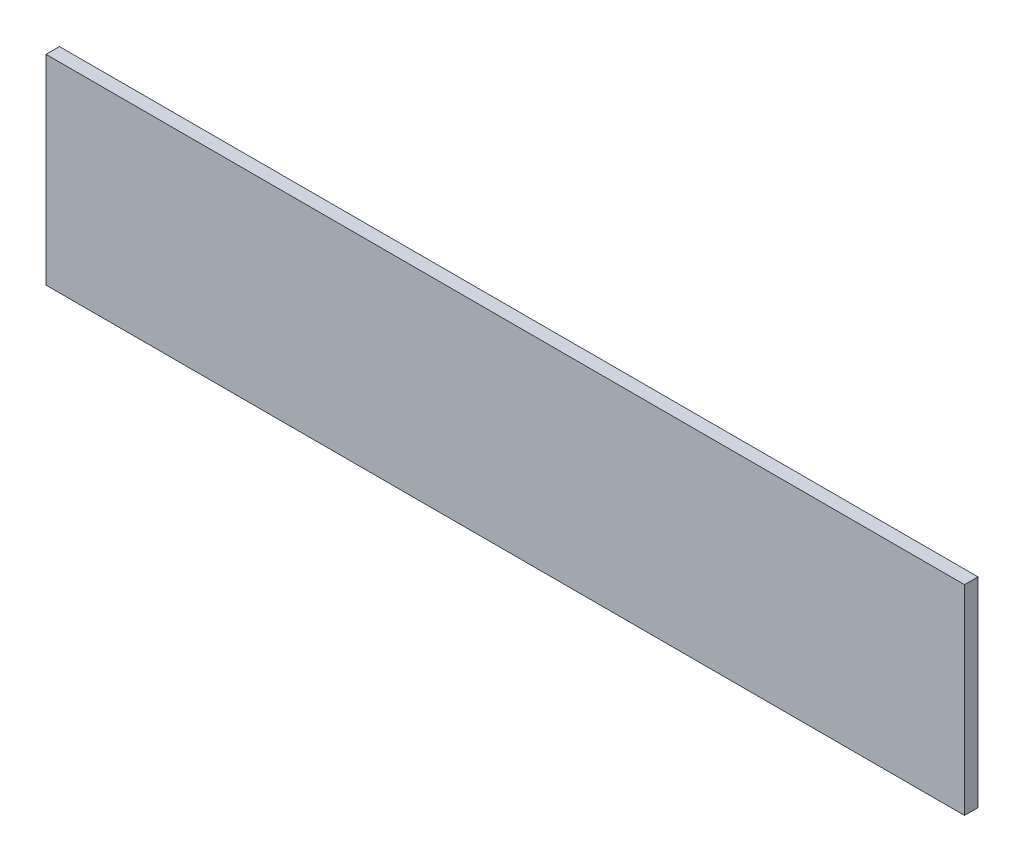
SolidWorks part; units mm, degrees
ref_plane "Plan de face" through (0, 0, 0) normal (0, 0, 1) x (1, 0, 0)
ref_plane "Plan de dessus" through (0, 0, 0) normal (0, 1, 0) x (1, 0, 0)
ref_plane "Plan de droite" through (0, 0, 0) normal (1, 0, 0) x (0, 0, -1)
sketch "Esquisse1" plane through (0, 0, 0) normal (0, 0, 1) x (1, 0, 0)
  line L1 (19.4828, -636.9004) -> (223.9828, -636.9004)
  line L2 (19.4828, -636.9004) -> (19.4828, -681.4004)
  line L3 (19.4828, -681.4004) -> (223.9828, -681.4004)
  line L4 (223.9828, -636.9004) -> (223.9828, -681.4004)
  dimension "D1" = 44.5
  dimension "D2" = 204.5
extrude "Boss.-Extru.1" add sketch "Esquisse1" along normal blind 3
